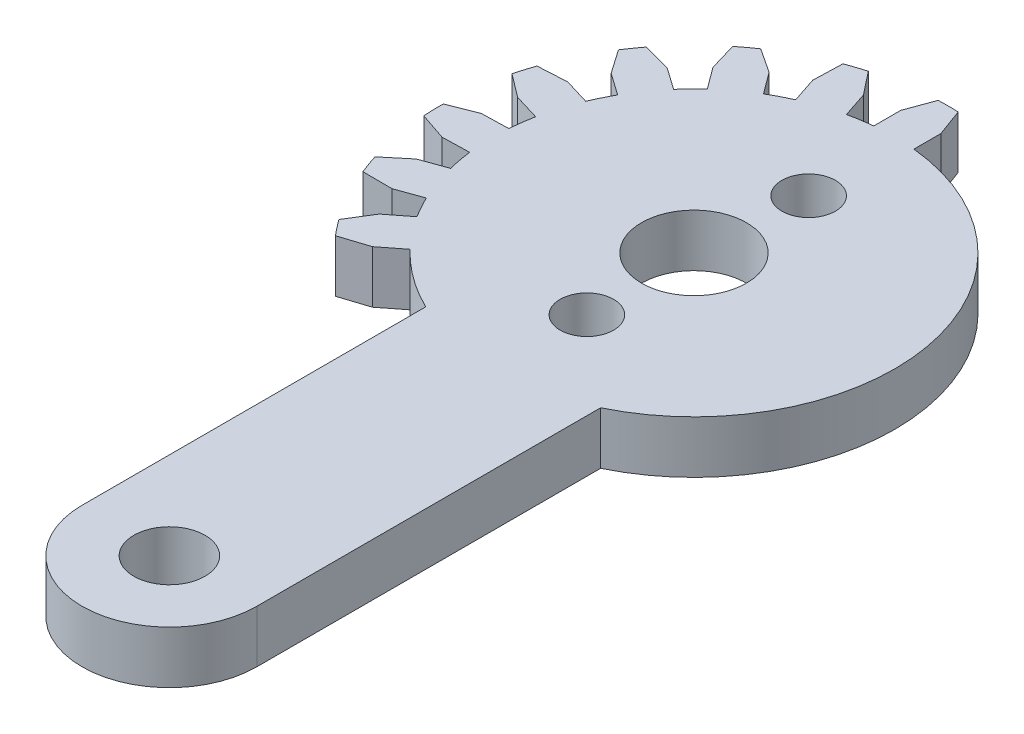
SolidWorks part; units mm, degrees
ref_plane "Alzado" through (0, 0, 0) normal (0, 0, 1) x (1, 0, 0)
ref_plane "Planta" through (0, 0, 0) normal (0, 1, 0) x (1, 0, 0)
ref_plane "Vista lateral" through (0, 0, 0) normal (1, 0, 0) x (0, 0, -1)
sketch "Croquis1" plane through (0, 0, 0) normal (0, 1, 0) x (1, 0, 0)
  line L0 (0, 0) -> (0, -30) construction
  line L1 (-5, -10.3395) -> (-5, -30)
  line L2 (5, -10.3395) -> (5, -30)
  line L5 (0, 0) -> (12.7, 0) construction
  arc A0 (5, -10.3395) -> (-5, -10.3395) centre (0, 0) ccw
  arc A1 (-5, -30) -> (5, -30) centre (0, -30) ccw
  circle A2 centre (0, -30) radius 2.0343
  circle A3 centre (0, 0) radius 3
  circle A4 centre (0, 0) radius 11.485 construction
  point P9 (0, 11.485)
  point P10 (0, -35)
  dimension "D1" = 22.97
  dimension "D3" = 30
  dimension "D2" = 10
  dimension "D4" = 6
extrude "Saliente-Extruir1" add sketch "Croquis1" along normal blind 3
sketch "Croquis3" plane through (0, 0, 0) normal (0, 1, 0) x (1, 0, 0)
  line L0 (0, 11.485) -> (0, 0) construction
  line L1 (0, 11.485) -> (0, 14.5475) construction
  line L2 (-1.1484, 12.9655) -> (-1.1484, 11.4274)
  line L3 (0.5742, 14.5362) -> (1.1484, 12.9655)
  line L4 (-0.5742, 14.5362) -> (-1.1484, 12.9655)
  line L5 (1.1484, 12.9655) -> (1.1484, 11.4274)
  line L6 (0, 0) -> (11.485, 0) construction
  circle A0 centre (0, 0) radius 14.5475 construction
  circle A1 centre (0, 0) radius 11.485 construction
  circle A2 centre (0, 0) radius 13.0162 construction
  arc A3 (5, -10.3395) -> (-5, -10.3395) centre (0, 0) ccw construction
  arc A4 (0.5742, 14.5362) -> (-0.5742, 14.5362) centre (0, 0) ccw
  arc A5 (1.1484, 11.4274) -> (-1.1484, 11.4274) centre (0, 0) ccw
  point P16 (0, 13.0162)
  dimension "D1" = 3.0625
  dimension "D2" = 1.1484
  dimension "D3" = 2.2969
extrude "Saliente-Extruir2" add sketch "Croquis3" along normal up to surface (3 mm away) up to face at (0, 3, 32.0343)
pattern_circular "MatrizC1" count 8 over 128 about axis through (0, 0, 0) along (0, 1, 0) of "Saliente-Extruir2"
sketch "Croquis4" plane through (0, 0, 0) normal (0, -1, 0) x (1, 0, 0)
  line L0 (0, 0) -> (0.6418, -8.7504) construction
  circle A0 centre (0.4481, -6.1086) radius 1.53
  circle A1 centre (0, 0) radius 6.125 construction
  circle A2 centre (0, 6.125) radius 1.53
  dimension "D1" = 3.06
  dimension "D2" = 12.25
extrude "Cortar-Extruir1" cut sketch "Croquis4" against normal blind 10
